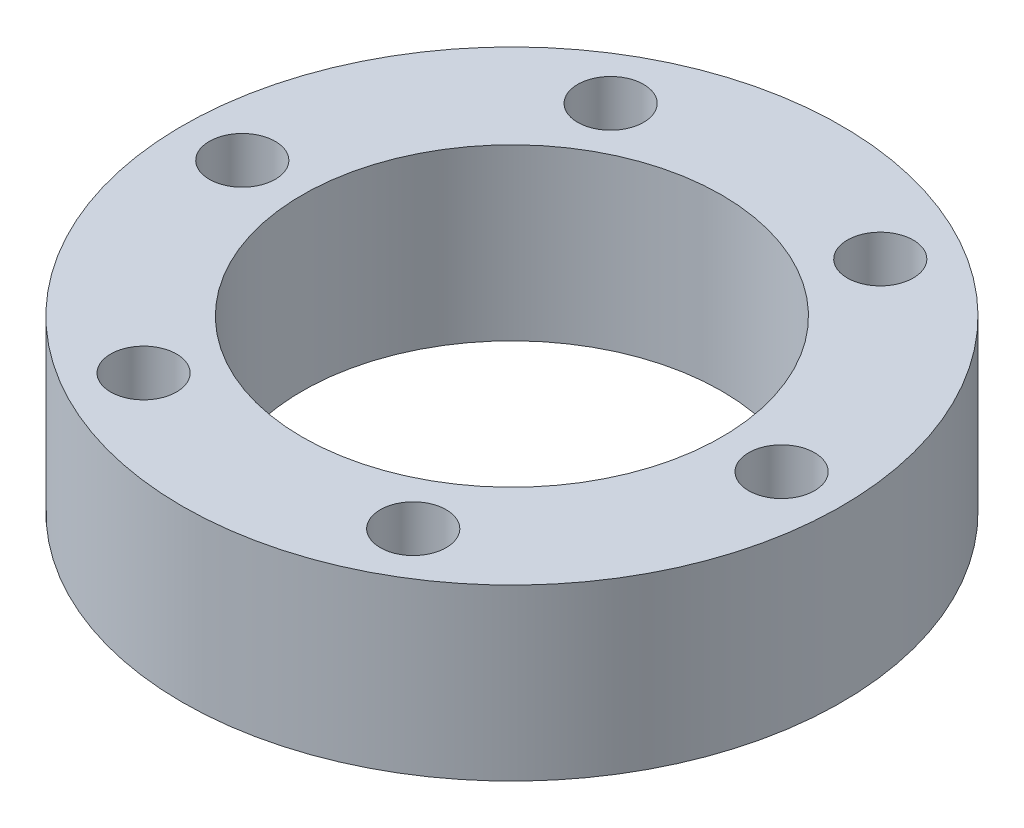
SolidWorks part; units mm, degrees
material "1.0036 (S235JRG1)"
ref_plane "Front Plane" through (0, 0, 0) normal (0, 0, 1) x (1, 0, 0)
ref_plane "Top Plane" through (0, 0, 0) normal (0, 1, 0) x (1, 0, 0)
ref_plane "Right Plane" through (0, 0, 0) normal (1, 0, 0) x (0, 0, -1)
sketch "Sketch1" plane through (0, 0, 0) normal (0, 1, 0) x (1, 0, 0)
  circle A0 centre (0, 0) radius 33
  circle A1 centre (0, 0) radius 21
  dimension "D1" = 42
  dimension "D2" = 12
extrude "Boss-Extrude1" add sketch "Sketch1" along normal blind 17
sketch "Sketch2" plane through (0, 17, 0) normal (0, 1, 0) x (1, 0, 0)
  point P0 (-27, 0)
  dimension "D1" = 27
hole_wizard "M6 Clearance Hole1" positions "3DSketch1" profile "Sketch4" hole size "M6" standard "ISO" end condition up to next
sketch3d "3DSketch1"
  point P0 (-27, 17, 0)
sketch "Sketch4" plane through (-27, 17, 0) normal (1, 0, 0) x (0, 0, 1)
  line L0 (0, 0) -> (0, 17)
  line L1 (0, 17) -> (3.3, 17)
  line L2 (3.3, 17) -> (3.3, 0)
  line L5 (3.3, 0) -> (0, 0)
  line L11 (0, -6.35) -> (0, 107.95) construction
  dimension "Thru Hole Dia." = 6.6
  dimension "Thru Hole Depth" = 17
pattern_circular "CirPattern1" count 6 over 360 about axis through (0, 0, 0) along (0, 1, 0) of "M6 Clearance Hole1"
